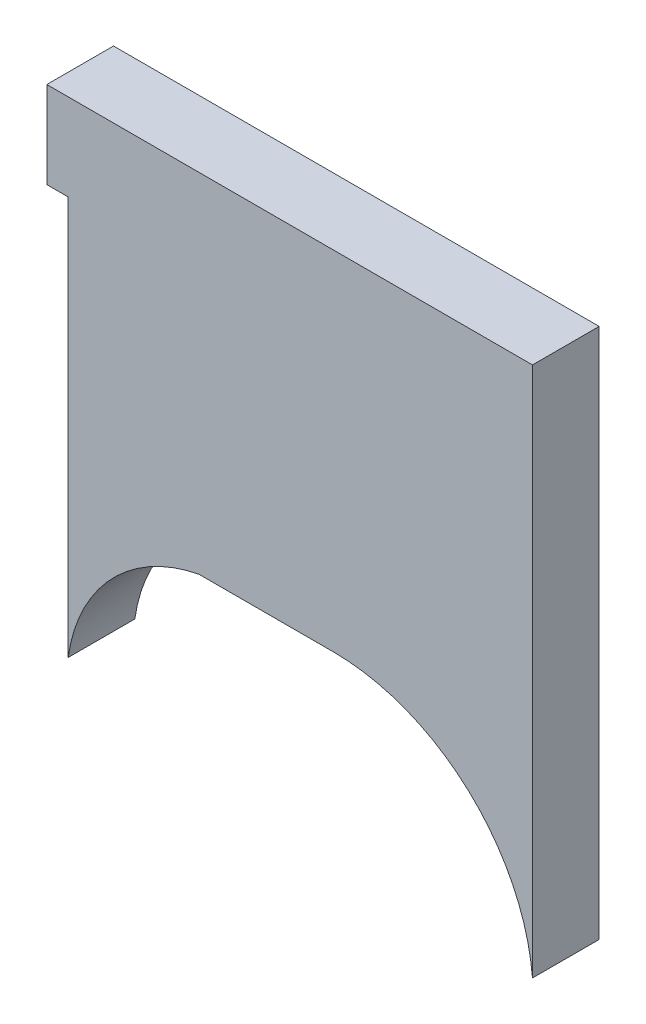
SolidWorks part; units mm, degrees
ref_plane "Front Plane" through (0, 0, 0) normal (0, 0, 1) x (1, 0, 0)
ref_plane "Top Plane" through (0, 0, 0) normal (0, 1, 0) x (1, 0, 0)
ref_plane "Right Plane" through (0, 0, 0) normal (1, 0, 0) x (0, 0, -1)
sketch "Sketch2" plane through (0, 0, 0) normal (0, 0, 1) x (1, 0, 0)
  line L1 (-53.2894, 44.6973) -> (-53.2894, 58.7269)
  line L2 (-53.2894, 44.6973) -> (-53.2894, 42.1573)
  line L3 (-69.1623, 42.1573) -> (-66.248, 42.1573)
  line L4 (-75.3929, 54.5994) -> (-76.408, 54.5994)
  line L5 (-76.408, 54.5994) -> (-76.408, 58.7269)
  line L6 (-76.408, 58.7269) -> (-54.5566, 58.7269)
  line L7 (-75.3929, 35.612) -> (-75.3929, 54.5994)
  line L8 (-53.2894, 33.452) -> (-53.2894, 42.1573)
  line L9 (-53.2894, 58.7269) -> (-54.5566, 58.7269)
  line L10 (-66.248, 42.1573) -> (-62.779, 42.1573)
  arc A0 (-62.779, 42.1573) -> (-53.2894, 33.452) centre (-62.779, 32.6323) cw
  arc A2 (-75.3929, 35.612) -> (-69.1623, 42.1573) centre (-67.7051, 34.532) cw
  dimension "D1" = 9.525
  dimension "D2" = 4.1275
extrude "Boss-Extrude1" add sketch "Sketch2" along normal blind 3.175
